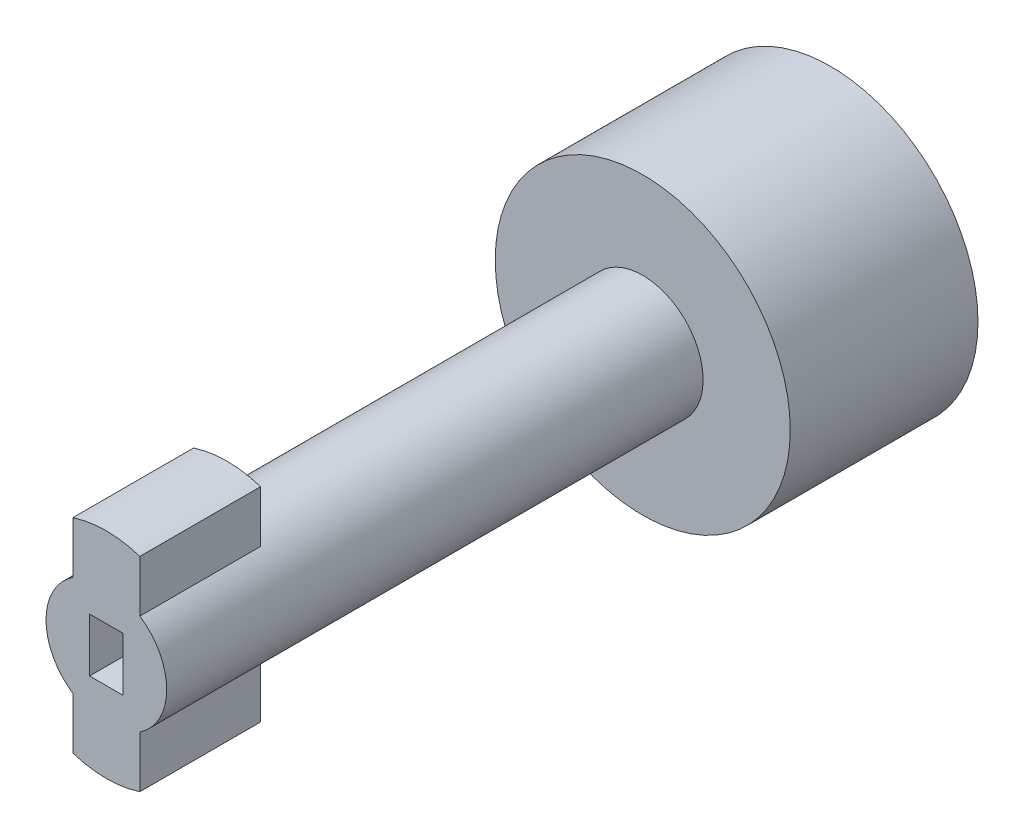
SolidWorks part; units mm, degrees
ref_plane "Alzado" through (0, 0, 0) normal (0, 0, 1) x (1, 0, 0)
ref_plane "Planta" through (0, 0, 0) normal (0, 1, 0) x (1, 0, 0)
ref_plane "Vista lateral" through (0, 0, 0) normal (1, 0, 0) x (0, 0, -1)
sketch "Croquis1" plane through (0, 0, 0) normal (0, 0, 1) x (1, 0, 0)
  circle A0 centre (0, 0) radius 4.5
  dimension "D1" = 9
extrude "Saliente-Extruir1" add sketch "Croquis1" along normal blind 25
sketch "Croquis2" plane through (0, 0, 25) normal (0, 0, 1) x (1, 0, 0)
  line L1 (-2.5, 8.5) -> (2.5, 8.5)
  line L2 (-2.5, 8.5) -> (-2.5, -8.5)
  line L3 (-2.5, -8.5) -> (2.5, -8.5)
  line L4 (2.5, 8.5) -> (2.5, -8.5)
  line L5 (-2.5, 8.5) -> (2.5, -8.5) construction
  line L6 (-2.5, -8.5) -> (2.5, 8.5) construction
  point P0 (0, 0)
  dimension "D1" = 17
  dimension "D2" = 5
extrude "Saliente-Extruir2" add sketch "Croquis2" against normal blind 9
sketch "Croquis3" plane through (0, 0, 25) normal (0, 0, 1) x (1, 0, 0)
  circle A0 centre (0, 0) radius 8
  circle A1 centre (0, 0) radius 11
  dimension "D1" = 22
  dimension "D2" = 16
extrude "Cortar-Extruir1" cut sketch "Croquis3" against normal blind 9
sketch "Croquis4" plane through (0, 0, 0) normal (0, 0, -1) x (-1, 0, 0)
  circle A0 centre (0, 0) radius 4.5
  dimension "D1" = 9
extrude "Saliente-Extruir4" add sketch "Croquis4" along normal blind 2
sketch "Croquis5" plane through (0, 0, -2) normal (0, 0, -1) x (-1, 0, 0)
  circle A0 centre (0, 0) radius 11
  dimension "D1" = 22
sketch "Croquis6" plane through (0, 0, 25) normal (0, 0, 1) x (1, 0, 0)
  line L1 (-1.25, 2) -> (1.25, 2)
  line L2 (-1.25, 2) -> (-1.25, -2)
  line L3 (-1.25, -2) -> (1.25, -2)
  line L4 (1.25, 2) -> (1.25, -2)
  line L5 (-1.25, 2) -> (1.25, -2) construction
  line L6 (-1.25, -2) -> (1.25, 2) construction
  point P0 (0, 0)
  dimension "D1" = 2.5
  dimension "D2" = 4
extrude "Cortar-Extruir2" cut sketch "Croquis6" against normal blind 5
sketch "Croquis8" plane through (0, 0, -2) normal (0, 0, -1) x (-1, 0, 0)
  circle A0 centre (0, 0) radius 4.5
extrude "Saliente-Extruir5" add sketch "Croquis8" along normal blind 13
sketch "Croquis9" plane through (0, 0, -15) normal (0, 0, -1) x (-1, 0, 0)
  circle A0 centre (0, 0) radius 11
  dimension "D1" = 22
extrude "Saliente-Extruir6" add sketch "Croquis9" along normal blind 14
